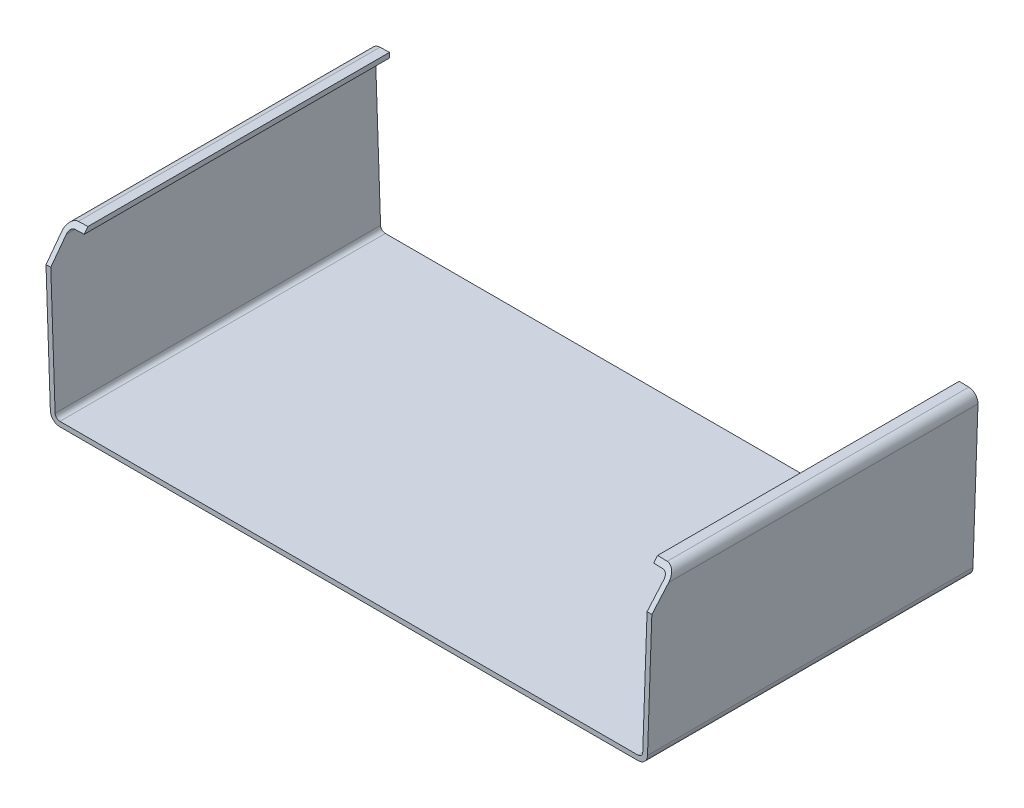
SolidWorks part; units mm, degrees
ref_plane "Front Plane" through (0, 0, 0) normal (0, 0, 1) x (1, 0, 0)
ref_plane "Top Plane" through (0, 0, 0) normal (0, 1, 0) x (1, 0, 0)
ref_plane "Right Plane" through (0, 0, 0) normal (1, 0, 0) x (0, 0, -1)
sketch "Sketch1" plane through (0, 0, 0) normal (0, 0, 1) x (1, 0, 0)
  line L0 (0, 0) -> (0, 50) construction
  line L1 (0, 0) -> (-60.5686, 0)
  line L2 (-62.5674, 1.9302) -> (-63.6232, 32.1615)
  line L3 (-61.6942, 34.2301) -> (-59.693, 34.3)
  line L4 (0, 1) -> (-60.5686, 1)
  line L5 (-61.568, 1.9651) -> (-62.6238, 32.1964)
  line L6 (-61.6593, 33.2307) -> (-59.6581, 33.3006)
  line L7 (-59.693, 34.3) -> (-59.6581, 33.3006)
  line L8 (59.693, 34.3) -> (59.6581, 33.3006)
  line L9 (61.6593, 33.2307) -> (59.6581, 33.3006)
  line L10 (61.568, 1.9651) -> (62.6238, 32.1964)
  line L11 (0, 1) -> (60.5686, 1)
  line L12 (61.6942, 34.2301) -> (59.693, 34.3)
  line L13 (62.5674, 1.9302) -> (63.6232, 32.1615)
  line L14 (0, 0) -> (60.5686, 0)
  arc A0 (-62.5674, 1.9302) -> (-60.5686, 0) centre (-60.5686, 2) ccw
  arc A1 (-61.6942, 34.2301) -> (-63.6232, 32.1615) centre (-61.6244, 32.2313) ccw
  arc A2 (-61.568, 1.9651) -> (-60.5686, 1) centre (-60.5686, 2) ccw
  arc A3 (-61.6593, 33.2307) -> (-62.6238, 32.1964) centre (-61.6244, 32.2313) ccw
  arc A4 (61.6593, 33.2307) -> (62.6238, 32.1964) centre (61.6244, 32.2313) cw
  arc A5 (61.568, 1.9651) -> (60.5686, 1) centre (60.5686, 2) cw
  arc A6 (61.6942, 34.2301) -> (63.6232, 32.1615) centre (61.6244, 32.2313) cw
  arc A7 (62.5674, 1.9302) -> (60.5686, 0) centre (60.5686, 2) cw
  point P0 (63.693, 34.1603)
  point P8 (-62.5, 0)
  point P11 (-63.693, 34.1603)
  point P31 (62.5, 0)
  dimension "D7" = 2
  dimension "D1" = 50
  dimension "D2" = 90
  dimension "D3" = 62.5
  dimension "D4" = 63.693
  dimension "D5" = 34.3
  dimension "D6" = 4
  dimension "D8" = 1
extrude "Boss-Extrude1" add sketch "Sketch1" along normal mid plane 68.2
sketch "Sketch2" plane through (62.4239, -2.1801, 0) normal (0.9994, -0.0349, 0) x (0, 0, -1)
  line L0 (-34.1, 36.3625) -> (34.1, 36.3625) construction
  line L1 (-34.1, 36.3625) -> (-34.1, 34.3625) construction
  line L2 (-34.1, 4.1128) -> (-34.1, 34.3625) construction
  line L3 (-34.1, 36.3625) -> (34.1, 36.3625) construction
  line L4 (-34.1, 36.3625) -> (-34.1, 34.3625) construction
  line L5 (-34.1, 4.1128) -> (-34.1, 34.3625) construction
  line L6 (-34.1, 36.3625) -> (-29.1, 36.3625)
  line L7 (-29.1, 36.3625) -> (-34.1, 30.1625)
  line L8 (-34.1, 30.1625) -> (-34.1, 36.3625)
  dimension "D1" = 5
  dimension "D2" = 6.2
extrude "Cut-Extrude1" cut sketch "Sketch2" against normal blind 7
mirror "Mirror1" about plane through (0, 0, 0) normal (1, 0, 0) of "Cut-Extrude1"
ref_plane "Plane1" through (-60.5686, 0, 0) normal (1, 0, 0) x (0, 0, -1)
sketch "Sketch6" plane through (0, 0, 0) normal (0, -1, 0) x (1, 0, 0)
  line L0 (-60.5686, 34.1) -> (-60.5686, -34.1) construction
  line L1 (60.5686, 34.1) -> (60.5686, -34.1) construction
  line L2 (-60.5686, 34.1) -> (-60.5686, -34.1) construction
  line L3 (60.5686, 34.1) -> (60.5686, -34.1) construction
  line L4 (0, 34.1) -> (0, -34.1) construction
  line L5 (-60.5686, 34.1) -> (60.5686, 34.1) construction
  circle A0 centre (25.05, -10.9) radius 2.55
  dimension "D5" = 5.1
  dimension "D1" = 121.1373
  dimension "D3" = 25.05
  dimension "D4" = 45
equation "\"D4@Sketch5\"=\"D3@Sketch5\"/2"
equation "\"D2@Sketch6\"=\"D1@Sketch6\"/2"
equation "\"D4@Sketch7\"=\"D2@Sketch7\"/2"
equation "\"D3@Sketch8\"=\"D2@Sketch8\"/2"
equation "\"D3@Sketch9\"=\"D2@Sketch9\"/2"
equation "\"D4@Sketch17\"  =\"D3@Sketch17\"/2"
equation "\"D2@Sketch18\"=\"D1@Sketch18\"/2"
equation "\"D6@Sketch18\"=\"D5@Sketch18\"/2"
